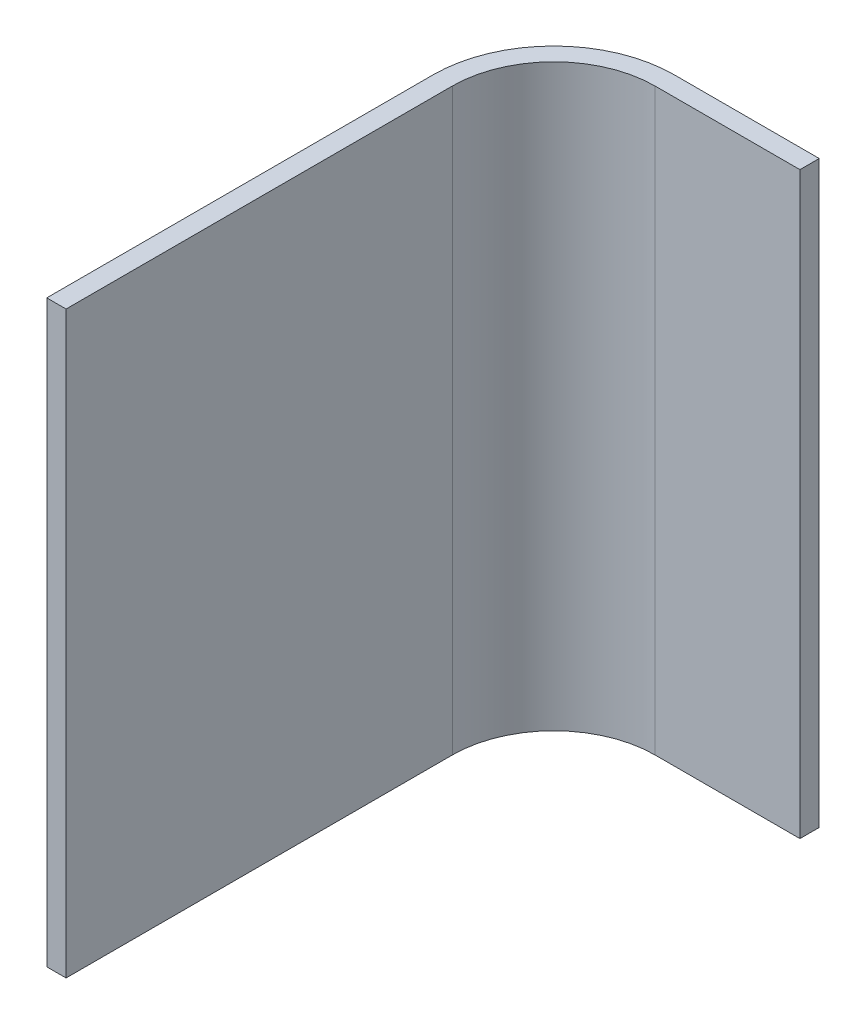
SolidWorks part; units mm, degrees
ref_plane "Alzado" through (0, 0, 0) normal (0, 0, 1) x (1, 0, 0)
ref_plane "Planta" through (0, 0, 0) normal (0, 1, 0) x (1, 0, 0)
ref_plane "Vista lateral" through (0, 0, 0) normal (1, 0, 0) x (0, 0, -1)
sketch "Croquis3" plane through (0, 0, 0) normal (0, 1, 0) x (1, 0, 0)
  line L0 (0, 0) -> (0, 80)
  line L1 (25, 105) -> (55, 105)
  arc A0 (0, 80) -> (25, 105) centre (25, 80) cw
  dimension "D3" = 25
  dimension "D1" = 80
  dimension "D2" = 30
extrude "Extruir-Lámina1" add sketch "Croquis3" along normal blind 120 thin
